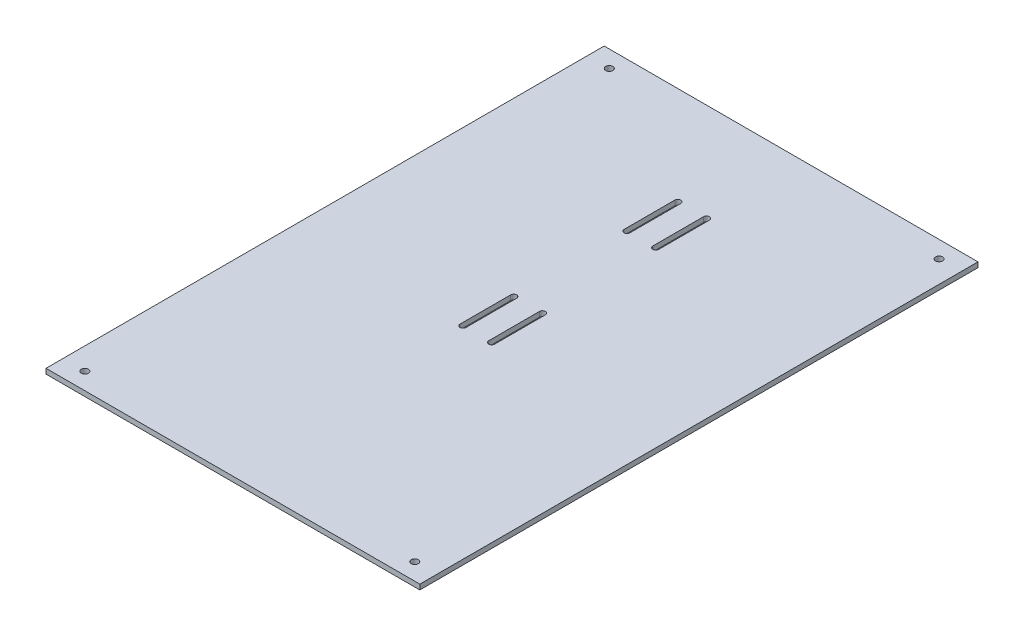
SolidWorks part; units mm, degrees
ref_plane "Front Plane" through (0, 0, 0) normal (0, 0, 1) x (1, 0, 0)
ref_plane "Top Plane" through (0, 0, 0) normal (0, 1, 0) x (1, 0, 0)
ref_plane "Right Plane" through (0, 0, 0) normal (1, 0, 0) x (0, 0, -1)
sketch "Sketch1" plane through (0, 0, 0) normal (1, 0, 0) x (0, 0, -1)
  line L0 (-207.5, -13) -> (122.5, -13)
extrude "Extrude-Thin1" add sketch "Sketch1" along normal up to vertex (110.5 mm away) and the other way up to vertex (110.5 mm away) thin thin type one direction reverse wall 3
sketch "Sketch2" plane through (0, -13, 0) normal (0, -1, 0) x (1, 0, 0)
  line L0 (-8.9932, -34.5) -> (-8.9932, -64.5) construction
  line L1 (-7.2432, -34.5) -> (-7.2432, -64.5)
  line L2 (-10.7432, -34.5) -> (-10.7432, -64.5)
  line L3 (8.0068, -34.5) -> (8.0068, -64.5) construction
  line L4 (9.7568, -34.5) -> (9.7568, -64.5)
  line L5 (6.2568, -34.5) -> (6.2568, -64.5)
  line L6 (8.0068, 62.5) -> (8.0068, 32.5) construction
  line L7 (9.7568, 62.5) -> (9.7568, 32.5)
  line L8 (6.2568, 62.5) -> (6.2568, 32.5)
  line L9 (-8.9932, 62.5) -> (-8.9932, 32.5) construction
  line L10 (-7.2432, 62.5) -> (-7.2432, 32.5)
  line L11 (-10.7432, 62.5) -> (-10.7432, 32.5)
  line L12 (-110.5, 207.5) -> (-110.5, -122.5) construction
  arc A0 (-7.2432, -34.5) -> (-10.7432, -34.5) centre (-8.9932, -34.5) ccw
  arc A1 (-10.7432, -64.5) -> (-7.2432, -64.5) centre (-8.9932, -64.5) ccw
  arc A2 (9.7568, -34.5) -> (6.2568, -34.5) centre (8.0068, -34.5) ccw
  arc A3 (6.2568, -64.5) -> (9.7568, -64.5) centre (8.0068, -64.5) ccw
  arc A4 (9.7568, 62.5) -> (6.2568, 62.5) centre (8.0068, 62.5) ccw
  arc A5 (6.2568, 32.5) -> (9.7568, 32.5) centre (8.0068, 32.5) ccw
  arc A6 (-7.2432, 62.5) -> (-10.7432, 62.5) centre (-8.9932, 62.5) ccw
  arc A7 (-10.7432, 32.5) -> (-7.2432, 32.5) centre (-8.9932, 32.5) ccw
  circle A8 centre (97.5, -112.5) radius 2.1
  circle A9 centre (-97.5, -112.5) radius 2.1
  circle A10 centre (97.5, 197.5) radius 2.1
  circle A11 centre (-97.5, 197.5) radius 2.1
  point P2 (-8.9932, -49.5)
  point P3 (0, 0)
  point P9 (8.0068, -49.5)
  point P12 (-8.5, -49.635)
  point P17 (8.0068, 47.5)
  point P20 (-8.9932, 47.5)
  point P25 (-8.9932, 47.5)
  point P41 (8.5, 48.5)
  point P42 (8.5, 47.5)
  point P43 (0, 0)
  point P44 (8.0068, -49.5)
  point P49 (8.0068, 47.5)
  point P51 (-8.9932, -49.5)
  dimension "D2" = 1.75
  dimension "D3" = 4.2
  dimension "D1" = 30
  dimension "D4" = 310
  dimension "D5" = 13
extrude "Cut-Extrude1" cut sketch "Sketch2" against normal up to next
